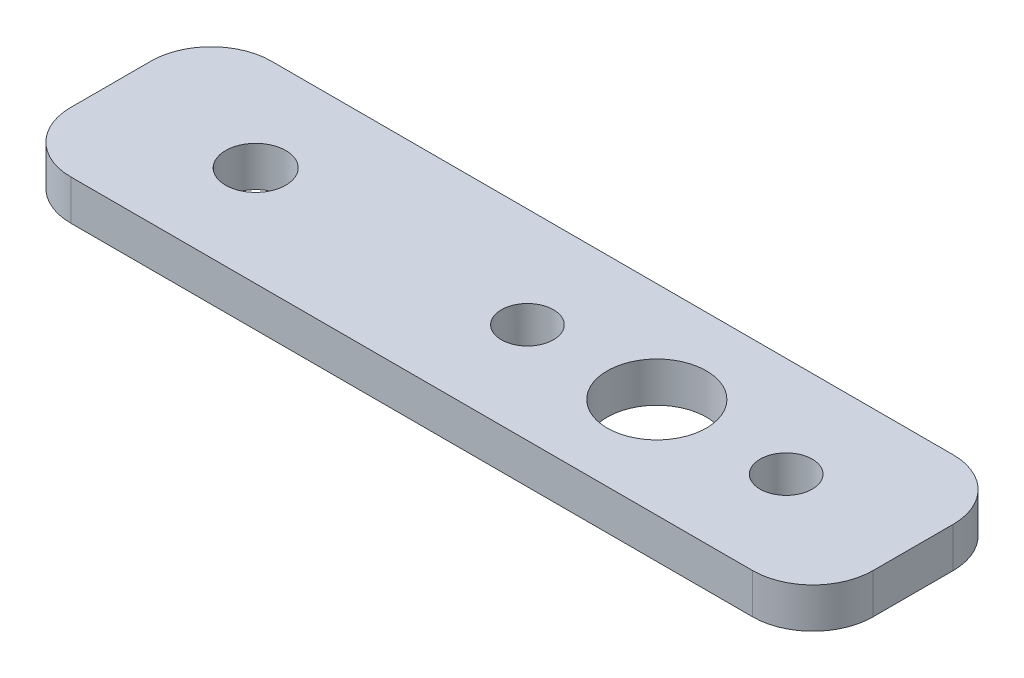
SolidWorks part; units mm, degrees
ref_plane "Front Plane" through (0, 0, 0) normal (0, 0, 1) x (1, 0, 0)
ref_plane "Top Plane" through (0, 0, 0) normal (0, 1, 0) x (1, 0, 0)
ref_plane "Right Plane" through (0, 0, 0) normal (1, 0, 0) x (0, 0, -1)
sketch "Sketch1" plane through (0, 0, 0) normal (0, 1, 0) x (1, 0, 0)
  line L1 (-20, 5) -> (20, 5)
  line L2 (-20, 5) -> (-20, -5)
  line L3 (-20, -5) -> (20, -5)
  line L4 (20, 5) -> (20, -5)
  line L5 (-20, 5) -> (20, -5) construction
  line L6 (-20, -5) -> (20, 5) construction
  point P0 (0, 0)
  dimension "D1" = 10
  dimension "D2" = 40
extrude "Boss-Extrude1" add sketch "Sketch1" along normal blind 2
sketch "Sketch2" plane through (0, 2, 0) normal (0, 1, 0) x (1, 0, 0)
  line L0 (7.2199, 5) -> (7.2199, -5) construction
  line L1 (-20, -5) -> (20, -5) construction
  circle A0 centre (7.2199, 0) radius 2.4729
  circle A1 centre (13.6699, 0) radius 1.3
  circle A3 centre (0.7699, 0) radius 1.3
  point P10 (7.2199, 0)
  dimension "D1" = 2.6
  dimension "D2" = 6.45
extrude "Cut-Extrude1" cut sketch "Sketch2" against normal blind 3
fillet "Fillet1" radius 3 4 edges at (20, 1, 5) (20, 1, -5) (-20, 1, -5) (-20, 1, 5)
hole_wizard "Ø3.0 (3) Diameter Hole1" positions "Sketch3" profile "Sketch4" hole size "Ø3.0" standard "BSI" end condition through all
sketch "Sketch3" plane through (0, 2, 0) normal (0, 1, 0) x (1, 0, 0)
  circle A0 centre (7.2199, 0) radius 2.4729 construction
  point P0 (-12.7801, 0)
  dimension "D1" = 20
sketch "Sketch4" plane through (-12.7801, 2, 0) normal (1, 0, 0) x (0, 0, 1)
  line L0 (0, 0) -> (0, 2)
  line L1 (0, 2) -> (1.5, 2)
  line L2 (1.5, 2) -> (1.5, 0)
  line L5 (1.5, 0) -> (0, 0)
  line L11 (0, -6.35) -> (0, 107.95) construction
  dimension "Thru Hole Dia." = 3
  dimension "Thru Hole Depth" = 2
